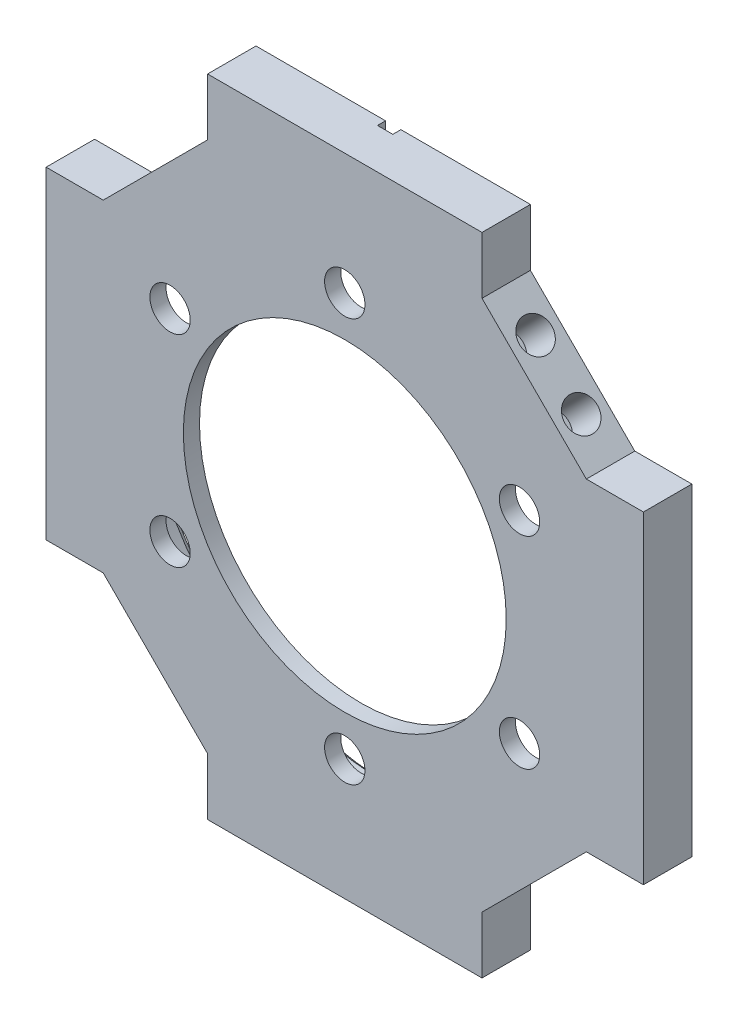
SolidWorks part; units mm, degrees
ref_plane "Front Plane" through (0, 0, 0) normal (0, 0, 1) x (1, 0, 0)
ref_plane "Top Plane" through (0, 0, 0) normal (0, 1, 0) x (1, 0, 0)
ref_plane "Right Plane" through (0, 0, 0) normal (1, 0, 0) x (0, 0, -1)
sketch "Sketch1" plane through (0, 0, 0) normal (0, 0, 1) x (1, 0, 0)
  line L1 (0, 0) -> (74, 0)
  line L2 (0, 0) -> (0, 80)
  line L3 (0, 80) -> (74, 80)
  line L4 (74, 0) -> (74, 80)
  circle A0 centre (37, 40) radius 30
  dimension "D3" = 60
  dimension "D1" = 74
  dimension "D2" = 80
extrude "Boss-Extrude1" add sketch "Sketch1" along normal blind 6
sketch "Sketch2" plane through (0, 0, 6) normal (0, 0, 1) x (1, 0, 0)
  circle A0 centre (37, 40) radius 30
  circle A1 centre (37, 40) radius 20
  dimension "D1" = 40
extrude "Boss-Extrude2" add sketch "Sketch2" against normal blind 2
sketch "Sketch3" plane through (0, 0, 4) normal (0, 0, -1) x (-1, 0, 0)
  circle A0 centre (-37, 65) radius 2.5
  circle A1 centre (-37, 40) radius 20 construction
  circle A2 centre (-15.3494, 52.5) radius 2.5
  circle A3 centre (-15.3494, 27.5) radius 2.5
  circle A4 centre (-37, 15) radius 2.5
  circle A5 centre (-58.6506, 27.5) radius 2.5
  circle A6 centre (-58.6506, 52.5) radius 2.5
  point P17 (-37, 40)
  dimension "D1" = 25
  dimension "D2" = 5
  dimension "D3" = 6
extrude "Cut-Extrude1" cut sketch "Sketch3" against normal blind 2
chamfer "Chamfer1" distance 20 angle 45 4 edges at (74, 0, 3) (0, 0, 3) (0, 80, 3) (74, 80, 3)
sketch "Sketch4" plane through (-30, 30, 0) normal (-0.7071, 0.7071, 0) x (0, 0, 1)
  line L0 (3, 60.5685) -> (3, 52.5685) construction
  line L2 (0, 42.4264) -> (0, 70.7107) construction
  line L3 (3, 56.5685) -> (0, 56.5685) construction
  circle A0 centre (3, 60.5685) radius 2
  circle A1 centre (3, 52.5685) radius 2
  point P4 (3, 56.5685)
  point P7 (0, 56.5685)
  dimension "D1" = 4
  dimension "D3" = 4
  dimension "D2" = 8
extrude "Cut-Extrude2" cut sketch "Sketch4" against normal blind 10
sketch "Sketch5" plane through (0, 0, 6) normal (0, 0, 1) x (1, 0, 0)
  line L0 (37, 80) -> (37, 71.5634) construction
  line L1 (54, 80) -> (20, 80) construction
ref_plane "Plane1" through (37, 0, 0) normal (-1, 0, 0) x (0, -1, 0)
mirror "Mirror1" about plane through (37, 0, 0) normal (-1, 0, 0) of "Cut-Extrude2"
sketch "Sketch6" plane through (0, 0, 6) normal (0, 0, 1) x (1, 0, 0)
  line L0 (0, 40) -> (8.6106, 40) construction
  line L1 (0, 60) -> (0, 20) construction
ref_plane "Plane2" through (0, 40, 0) normal (0, -1, 0) x (1, 0, 0)
mirror "Mirror2" about plane through (0, 40, 0) normal (0, -1, 0) of "Cut-Extrude2", "Mirror1"
chamfer "Chamfer2" distance 1 angle 45 1 edges at (67, 40, 0)
sketch "Sketch7" plane through (0, 0, 0) normal (0, 0, -1) x (-1, 0, 0)
  line L0 (-54, 80) -> (-20, 80) construction
  line L1 (-37.9524, 75.5732) -> (-36.0476, 75.5732)
  line L2 (-37.9524, 75.5732) -> (-37.9524, 80)
  line L3 (-37.9524, 80) -> (-36.0476, 80)
  line L4 (-36.0476, 75.5732) -> (-36.0476, 80)
  line L5 (-37.9524, 75.5732) -> (-36.0476, 80) construction
  line L6 (-37.9524, 80) -> (-36.0476, 75.5732) construction
  point P0 (-37, 77.7866)
extrude "Cut-Extrude3" cut sketch "Sketch7" against normal blind 1
sketch "Sketch8" plane through (0, 0, 6) normal (0, 0, 1) x (1, 0, 0)
  line L0 (0, 60) -> (7.0711, 60)
  line L1 (7.0711, 60) -> (20, 72.9289)
  line L2 (20, 72.9289) -> (20, 80)
  line L3 (20, 80) -> (0, 60) construction
  line L4 (0, 60) -> (20, 80)
  line L5 (54, 80) -> (54, 72.9289)
  line L6 (54, 72.9289) -> (66.9289, 60)
  line L7 (66.9289, 60) -> (74, 60)
  line L8 (74, 60) -> (54, 80)
  line L9 (0, 40) -> (8.2422, 40) construction
  line L10 (0, 60) -> (0, 20) construction
  line L11 (66.9289, 20) -> (74, 20)
  line L12 (54, 7.0711) -> (66.9289, 20)
  line L13 (54, 0) -> (54, 7.0711)
  line L14 (74, 20) -> (54, 0)
  line L15 (0, 20) -> (7.0711, 20)
  line L16 (7.0711, 20) -> (20, 7.0711)
  line L17 (20, 7.0711) -> (20, 0)
  line L18 (0, 20) -> (20, 0)
  dimension "D1" = 5
extrude "Cut-Extrude4" cut sketch "Sketch8" against normal through all
